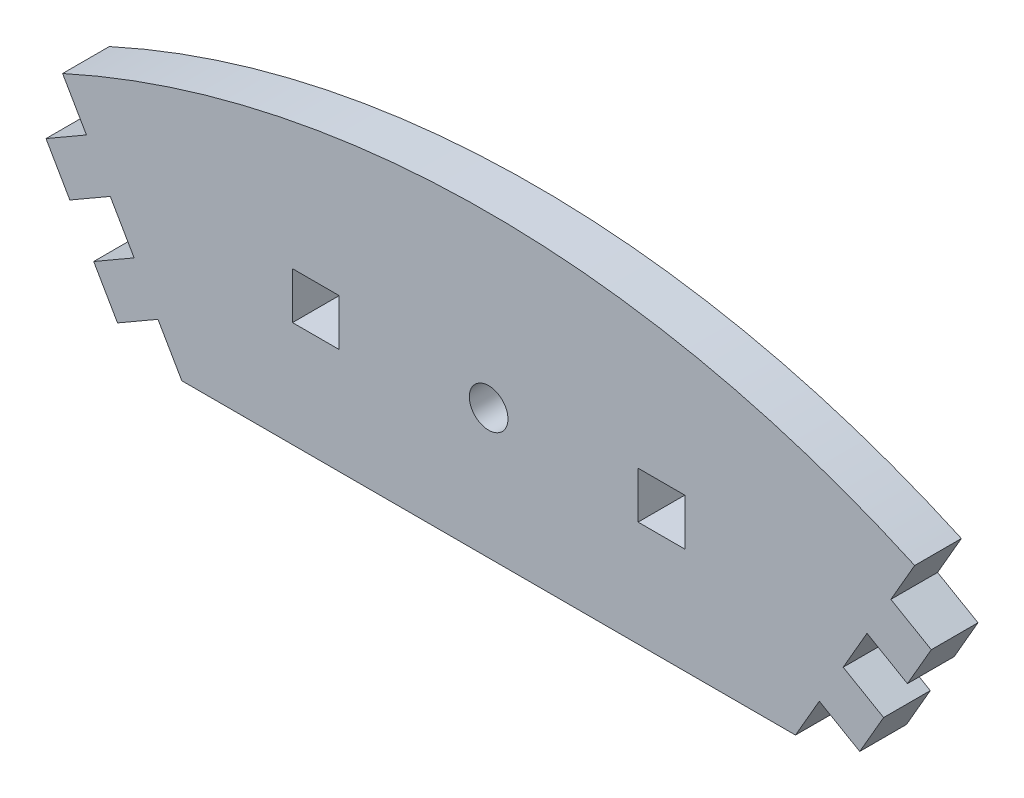
SolidWorks part; units mm, degrees
ref_plane "Front Plane" through (0, 0, 0) normal (0, 0, 1) x (1, 0, 0)
ref_plane "Top Plane" through (0, 0, 0) normal (0, 1, 0) x (1, 0, 0)
ref_plane "Right Plane" through (0, 0, 0) normal (1, 0, 0) x (0, 0, -1)
sketch "Sketch1" plane through (0, 0, 0) normal (0, 0, 1) x (1, 0, 0)
  line L0 (-32.85, 77.9867) -> (32.85, 77.9867)
  line L4 (-32.85, 77.9867) -> (-35.403, 82.4086)
  line L5 (0, 0) -> (0, 126.1957) construction
  line L7 (32.85, 77.9867) -> (35.403, 82.4086)
  line L8 (35.403, 82.4086) -> (39.7331, 79.9086)
  line L9 (39.7331, 79.9086) -> (42.2861, 84.3305)
  line L10 (42.2861, 84.3305) -> (37.956, 86.8305)
  line L11 (37.956, 86.8305) -> (40.509, 91.2525)
  line L12 (40.509, 91.2525) -> (44.8391, 88.7525)
  line L13 (44.8391, 88.7525) -> (47.3921, 93.1744)
  line L14 (47.3921, 93.1744) -> (43.062, 95.6744)
  line L15 (43.062, 95.6744) -> (45.615, 100.0963)
  line L16 (-43.062, 95.6744) -> (-45.615, 100.0963)
  line L17 (-47.3921, 93.1744) -> (-43.062, 95.6744)
  line L18 (-44.8391, 88.7525) -> (-47.3921, 93.1744)
  line L19 (-40.509, 91.2525) -> (-44.8391, 88.7525)
  line L20 (-37.956, 86.8305) -> (-40.509, 91.2525)
  line L21 (-42.2861, 84.3305) -> (-37.956, 86.8305)
  line L22 (-39.7331, 79.9086) -> (-42.2861, 84.3305)
  line L23 (-35.403, 82.4086) -> (-39.7331, 79.9086)
  arc A0 (-45.615, 100.0963) -> (45.615, 100.0963) centre (0, 0) cw
  dimension "D1" = 120
  dimension "D2" = 110
  dimension "D3" = 25.53
  dimension "D4" = 5
  dimension "D5" = 65.7
extrude "Boss-Extrude1" add sketch "Sketch1" along normal blind 5
sketch "Sketch2" plane through (0, 0, 5) normal (0, 0, 1) x (1, 0, 0)
  line L0 (0, 111.5372) -> (0, 71.5875) construction
  line L1 (0, -2.75) -> (0, 2.75) construction
  line L3 (16, 94.3078) -> (21, 94.3078)
  line L4 (16, 94.3078) -> (16, 89.3078)
  line L5 (16, 89.3078) -> (21, 89.3078)
  line L6 (21, 94.3078) -> (21, 89.3078)
  line L11 (-32.85, 77.9867) -> (-17.0875, 77.9867) construction
  line L12 (-32.85, 77.9867) -> (32.85, 77.9867) construction
  line L14 (-16, 89.3078) -> (-21, 89.3078)
  line L15 (-16, 89.3078) -> (-16, 94.3078)
  line L16 (-16, 94.3078) -> (-21, 94.3078)
  line L17 (-21, 89.3078) -> (-21, 94.3078)
  circle A0 centre (0, 91.8974) radius 2.0675
  dimension "D4" = 4.135
  dimension "D1" = 32
  dimension "D2" = 5
  dimension "D3" = 5
  dimension "D5" = 16
  dimension "D7" = 5
extrude "Cut-Extrude1" cut sketch "Sketch2" against normal through all
